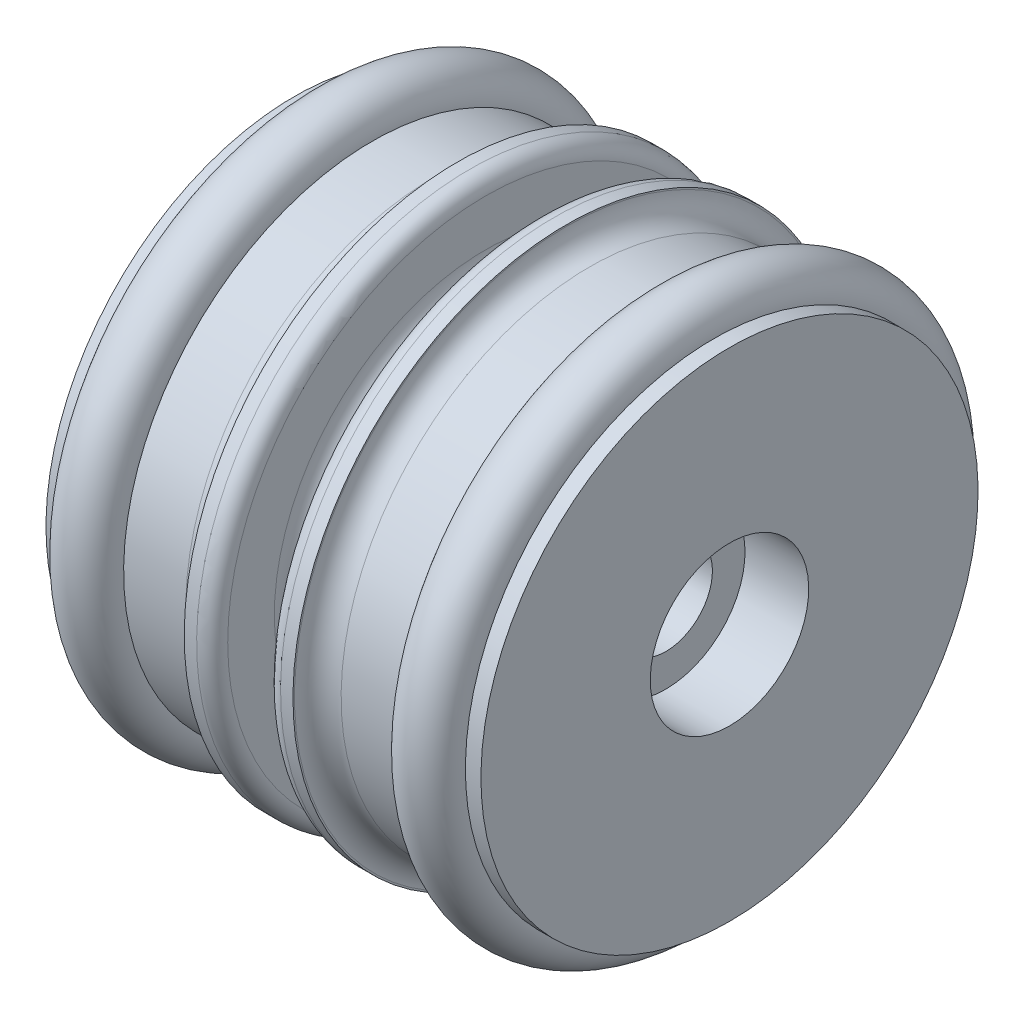
SolidWorks part; units mm, degrees
ref_plane "前视基准面" through (0, 0, 0) normal (0, 0, 1) x (1, 0, 0)
ref_plane "上视基准面" through (0, 0, 0) normal (0, 1, 0) x (1, 0, 0)
ref_plane "右视基准面" through (0, 0, 0) normal (1, 0, 0) x (0, 0, -1)
sketch "草图1" plane through (0, 0, 0) normal (0, 0, 1) x (1, 0, 0)
  line L0 (17.8004, 17.5) -> (17.8004, 17.6)
  line L1 (4.4004, 3) -> (24.2004, 3)
  line L2 (5.3004, 16) -> (9.3004, 16)
  line L3 (14.1004, 12.1) -> (14.5004, 12.1)
  line L4 (0.3004, 16) -> (1.3004, 16)
  line L5 (0.3004, 5.1) -> (4.4004, 5.1)
  line L6 (4.4004, 5.1) -> (4.4004, 3)
  line L7 (0, 0) -> (4.5, 0) construction
  line L8 (24.2004, 3) -> (24.2004, 5.1)
  line L9 (24.2004, 5.1) -> (28.3004, 5.1)
  line L10 (10.8004, 17.6) -> (10.8004, 17.5)
  line L12 (16.0004, 13.6) -> (16.0004, 16.6)
  line L13 (12.6004, 13.6) -> (12.6004, 16.6)
  line L14 (0.3004, 16) -> (0.3004, 5.1)
  line L15 (10.8004, 17.6) -> (11.6004, 17.6)
  line L16 (17.0004, 17.6) -> (17.8004, 17.6)
  line L18 (27.3004, 16) -> (28.3004, 16)
  line L19 (19.3004, 16) -> (23.3004, 16)
  line L34 (28.3004, 16) -> (28.3004, 5.1)
  arc A0 (1.3004, 16) -> (5.3004, 16) centre (3.3004, 16) ccw
  arc A1 (12.6004, 16.6) -> (11.6004, 17.6) centre (11.6004, 16.6) ccw
  arc A2 (23.3004, 16) -> (27.3004, 16) centre (25.3004, 16) ccw
  arc A3 (16.0004, 16.6) -> (17.0004, 17.6) centre (17.0004, 16.6) cw
  arc A4 (14.5004, 12.1) -> (16.0004, 13.6) centre (14.5004, 13.6) ccw
  arc A5 (14.1004, 12.1) -> (12.6004, 13.6) centre (14.1004, 13.6) cw
  arc A6 (17.8004, 17.5) -> (19.3004, 16) centre (19.3004, 17.5) ccw
  arc A7 (10.8004, 17.5) -> (9.3004, 16) centre (9.3004, 17.5) cw
  circle A8 centre (3.3004, 16) radius 1.95
  circle A9 centre (25.3004, 16) radius 1.95
  point P1 (0, 14)
  point P2 (2, 15)
  point P3 (4, 15.5)
  point P10 (4, 9.1086)
  point P20 (18.25, 9.1586)
  point P22 (17.8004, 16.2289)
  point P23 (18.25, 18.6076)
  point P24 (9.05, 9.1086)
  point P25 (9.05, 18.5576)
  point P31 (23.3, 15.5)
  point P32 (23.3, 9.1586)
  point P41 (10.8004, 16)
  point P44 (17.8004, 16)
  point P50 (16.0004, 17.6)
  dimension "D2" = 3
  dimension "D10" = 1
  dimension "D5" = 4.1
  dimension "D6" = 1.5
  dimension "D18" = 1.5
  dimension "D7" = 2
  dimension "D12" = 2
  dimension "D17" = 3
  dimension "D13" = 1
  dimension "D15" = 9.3
  dimension "D11" = 4
  dimension "D16" = 3
  dimension "D24" = 3.9
  dimension "D19" = 1.5
  dimension "D25" = 3.9
  dimension "D3" = 22
  dimension "D4" = 5.1
  dimension "D8" = 5.1
  dimension "D9" = 16
  dimension "D14" = 16
  dimension "D20" = 1
  dimension "D22" = 3.4
  dimension "D23" = 4.1
  dimension "D21" = 0.8
revolve "旋转1" add sketch "草图1" angle 360 about L7
